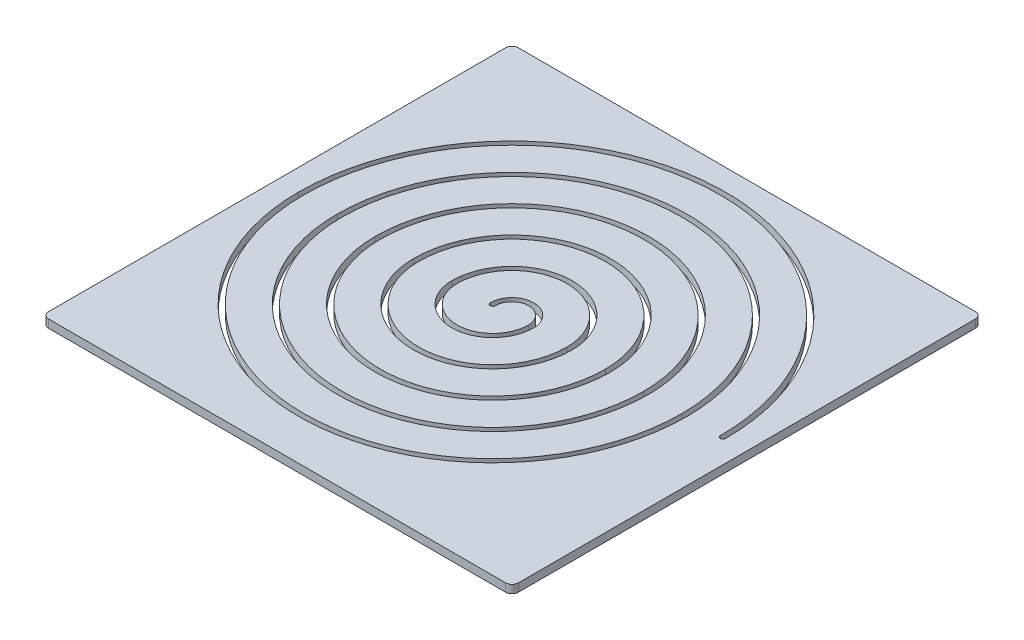
SolidWorks part; units mm, degrees
material "STARBOARD"
ref_plane "Plan de face" through (0, 0, 0) normal (0, 0, 1) x (1, 0, 0)
ref_plane "Plan de dessus" through (0, 0, 0) normal (0, 1, 0) x (1, 0, 0)
ref_plane "Plan de droite" through (0, 0, 0) normal (1, 0, 0) x (0, 0, -1)
sketch "Esquisse1" plane through (0, 0, 0) normal (0, 1, 0) x (1, 0, 0)
  line L0 (0, 0) -> (0, 413.3713) construction
  line L1 (-357.5, 367.5) -> (357.5, 367.5)
  line L2 (-367.5, 357.5) -> (-367.5, -357.5)
  line L3 (-357.5, -367.5) -> (357.5, -367.5)
  line L4 (367.5, 357.5) -> (367.5, -357.5)
  line L5 (0, 0) -> (554.1235, 0) construction
  arc A0 (-367.5, -357.5) -> (-357.5, -367.5) centre (-357.5, -357.5) ccw
  arc A1 (357.5, -367.5) -> (367.5, -357.5) centre (357.5, -357.5) ccw
  arc A2 (357.5, 367.5) -> (367.5, 357.5) centre (357.5, 357.5) cw
  arc A3 (-357.5, 367.5) -> (-367.5, 357.5) centre (-357.5, 357.5) ccw
  dimension "D2" = 10
  dimension "D1" = 735
extrude "Boss.-Extru.1" add sketch "Esquisse1" along normal blind 12.7
sketch "Esquisse2" plane through (0, 12.7, 0) normal (0, 1, 0) x (1, 0, 0)
  line L0 (0, 0) -> (0, 367.5) construction
  line L1 (357.5, 367.5) -> (-357.5, 367.5) construction
  line L2 (0, 0) -> (367.5, 0) construction
  line L3 (367.5, -357.5) -> (367.5, 357.5) construction
  line L4 (0, 0) -> (0, -367.5) construction
  line L5 (-357.5, -367.5) -> (357.5, -367.5) construction
  line L7 (0, 0) -> (-367.5, 0) construction
  line L8 (-367.5, 357.5) -> (-367.5, -357.5) construction
  arc A0 (30, 0) -> (-30, 0) centre (0, 0) ccw construction
  arc A1 (30, 0) -> (-90, 0) centre (-30, 0) cw construction
  arc A2 (-90, 0) -> (90, 0) centre (0, 0) cw construction
  arc A3 (90, 0) -> (-150, 0) centre (-30, 0) cw construction
  arc A4 (-150, 0) -> (150, 0) centre (0, 0) cw construction
  arc A5 (150, 0) -> (-210, 0) centre (-30, 0) cw construction
  arc A6 (-210, 0) -> (210, 0) centre (0, 0) cw construction
  arc A7 (210, 0) -> (-270, 0) centre (-30, 0) cw construction
  arc A8 (-270, 0) -> (270, 0) centre (0, 0) cw construction
  arc A9 (270, 0) -> (-330, 0) centre (-30, 0) cw construction
  arc A10 (-330, 0) -> (330, 0) centre (0, 0) cw construction
  arc A11 (26, 0) -> (-26, 0) centre (0, 0) ccw
  arc A12 (26, 0) -> (-86, 0) centre (-30, 0) cw
  arc A13 (-86, 0) -> (86, 0) centre (0, 0) cw
  arc A14 (86, 0) -> (-146, 0) centre (-30, 0) cw
  arc A15 (-146, 0) -> (146, 0) centre (0, 0) cw
  arc A16 (146, 0) -> (-206, 0) centre (-30, 0) cw
  arc A17 (-206, 0) -> (206, 0) centre (0, 0) cw
  arc A18 (206, 0) -> (-266, 0) centre (-30, 0) cw
  arc A19 (-266, 0) -> (266, 0) centre (0, 0) cw
  arc A20 (266, 0) -> (-326, 0) centre (-30, 0) cw
  arc A21 (-326, 0) -> (326, 0) centre (0, 0) cw
  arc A22 (34, 0) -> (-34, 0) centre (0, 0) ccw
  arc A23 (34, 0) -> (-94, 0) centre (-30, 0) cw
  arc A24 (-94, 0) -> (94, 0) centre (0, 0) cw
  arc A25 (94, 0) -> (-154, 0) centre (-30, 0) cw
  arc A26 (-154, 0) -> (154, 0) centre (0, 0) cw
  arc A27 (154, 0) -> (-214, 0) centre (-30, 0) cw
  arc A28 (-214, 0) -> (214, 0) centre (0, 0) cw
  arc A29 (214, 0) -> (-274, 0) centre (-30, 0) cw
  arc A30 (-274, 0) -> (274, 0) centre (0, 0) cw
  arc A31 (274, 0) -> (-334, 0) centre (-30, 0) cw
  arc A32 (-334, 0) -> (334, 0) centre (0, 0) cw
  arc A33 (-26, 0) -> (-34, 0) centre (-30, 0) cw
  arc A34 (326, 0) -> (334, 0) centre (330, 0) ccw
  dimension "D1" = 30
  dimension "D2" = 4
  dimension "D3" = 4
extrude "Enlèv. mat.-Extru.1" cut sketch "Esquisse2" against normal through all
